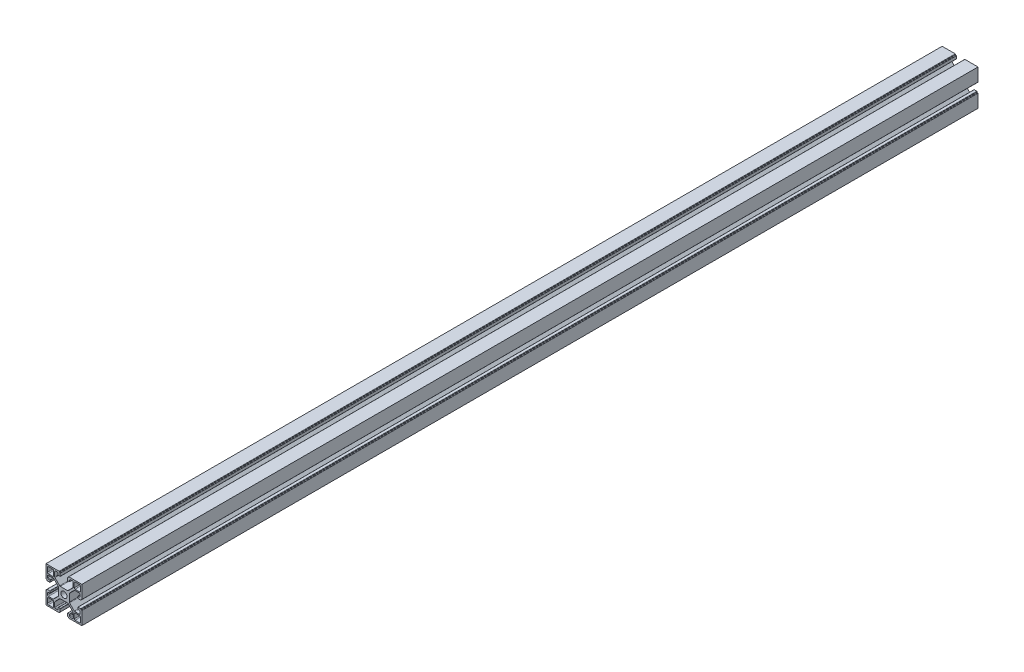
SolidWorks part; units mm, degrees
material "6063 T5"
ref_plane "Спереди" through (0, 0, 0) normal (0, 0, 1) x (1, 0, 0)
ref_plane "Сверху" through (0, 0, 0) normal (0, 1, 0) x (1, 0, 0)
ref_plane "Справа" through (0, 0, 0) normal (1, 0, 0) x (0, 0, -1)
sketch "Эскиз1" plane through (0, 0, 0) normal (0, 0, 1) x (1, 0, 0)
  line L0 (-19.98, 20.5457) -> (20.02, 20.5457) construction
  line L1 (-20, 10.25) -> (-20, 20)
  line L2 (-20, 20) -> (-10.25, 20)
  line L3 (10.25, 20) -> (20, 20)
  line L4 (-12.5, 11.5) -> (-17.5, 11.5)
  line L5 (-11.5, 12.5) -> (-11.5, 17.5)
  line L6 (-12.5, 18.5) -> (-17.5, 18.5)
  line L7 (-18.5, 12.5) -> (-18.5, 17.5)
  line L8 (20, 20) -> (20, 10.25)
  line L9 (11.5, 12.5) -> (11.5, 17.5)
  line L10 (12.5, 11.5) -> (17.5, 11.5)
  line L11 (18.5, 12.5) -> (18.5, 17.5)
  line L12 (12.5, 18.5) -> (17.5, 18.5)
  line L13 (20, -10.25) -> (20, -20)
  line L14 (20, -20) -> (10.25, -20)
  line L15 (12.5, -11.5) -> (17.5, -11.5)
  line L16 (11.5, -12.5) -> (11.5, -17.5)
  line L17 (12.5, -18.5) -> (17.5, -18.5)
  line L18 (18.5, -12.5) -> (18.5, -17.5)
  line L19 (-10.25, -20) -> (-20, -20)
  line L20 (-20, -20) -> (-20, -10.25)
  line L21 (-11.5, -12.5) -> (-11.5, -17.5)
  line L22 (-12.5, -11.5) -> (-17.5, -11.5)
  line L23 (-18.5, -12.5) -> (-18.5, -17.5)
  line L24 (-12.5, -18.5) -> (-17.5, -18.5)
  line L25 (0, 0) -> (-11.5, 12.5) construction
  line L26 (-20.032, 22.6558) -> (19.968, 22.6558) construction
  arc A1 (-17.5, 18.5) -> (-18.5, 17.5) centre (-17.5, 17.5) ccw
  arc A2 (-17.5, 11.5) -> (-18.5, 12.5) centre (-17.5, 12.5) cw
  arc A3 (-12.5, 11.5) -> (-11.5, 12.5) centre (-12.5, 12.5) ccw
  arc A4 (-11.5, 17.5) -> (-12.5, 18.5) centre (-12.5, 17.5) ccw
  circle A5 centre (0, 0) radius 3.4
  arc A7 (18.5, 17.5) -> (17.5, 18.5) centre (17.5, 17.5) ccw
  arc A8 (11.5, 17.5) -> (12.5, 18.5) centre (12.5, 17.5) cw
  arc A9 (11.5, 12.5) -> (12.5, 11.5) centre (12.5, 12.5) ccw
  arc A10 (17.5, 11.5) -> (18.5, 12.5) centre (17.5, 12.5) ccw
  arc A12 (17.5, -18.5) -> (18.5, -17.5) centre (17.5, -17.5) ccw
  arc A13 (17.5, -11.5) -> (18.5, -12.5) centre (17.5, -12.5) cw
  arc A14 (12.5, -11.5) -> (11.5, -12.5) centre (12.5, -12.5) ccw
  arc A15 (11.5, -17.5) -> (12.5, -18.5) centre (12.5, -17.5) ccw
  arc A17 (-18.5, -17.5) -> (-17.5, -18.5) centre (-17.5, -17.5) ccw
  arc A18 (-11.5, -17.5) -> (-12.5, -18.5) centre (-12.5, -17.5) cw
  arc A19 (-11.5, -12.5) -> (-12.5, -11.5) centre (-12.5, -12.5) ccw
  arc A20 (-17.5, -11.5) -> (-18.5, -12.5) centre (-17.5, -12.5) ccw
  point P5 (0, 0)
  line B0 (-20, 10.25) -> (-20, 5.4)
  line B1 (-19.7, 5.1) -> (-19.3, 5.1)
  line B2 (-19, 4.8) -> (-19, 4.4)
  line B3 (-18.7, 4.1) -> (-15.8, 4.1)
  line B4 (-15.5, 4.4) -> (-15.5, 6.1)
  line B5 (-15.8, 6.4) -> (-17.2, 6.4)
  line B6 (-18.2, 7.4) -> (-18.2, 9.25)
  line B7 (-17.2, 10.25) -> (-12.1642, 10.25)
  line B8 (-11.4571, 9.9571) -> (-6.2929, 4.7929)
  line B9 (-6, 4.0858) -> (-6, -4.0858)
  line B10 (-6, 0) -> (-20, 0) construction
  line B11 (-11.4571, -9.9571) -> (-6.2929, -4.7929)
  line B12 (-17.2, -10.25) -> (-12.1642, -10.25)
  line B13 (-18.2, -7.4) -> (-18.2, -9.25)
  line B14 (-15.8, -6.4) -> (-17.2, -6.4)
  line B15 (-15.5, -4.4) -> (-15.5, -6.1)
  line B16 (-18.7, -4.1) -> (-15.8, -4.1)
  line B17 (-19, -4.8) -> (-19, -4.4)
  line B18 (-19.7, -5.1) -> (-19.3, -5.1)
  line B19 (-20, -10.25) -> (-20, -5.4)
  arc B20 (-15.5, 6.1) -> (-15.8, 6.4) centre (-15.8, 6.1) ccw
  arc B21 (-15.8, 4.1) -> (-15.5, 4.4) centre (-15.8, 4.4) ccw
  arc B22 (-19, 4.4) -> (-18.7, 4.1) centre (-18.7, 4.4) ccw
  arc B23 (-19.3, 5.1) -> (-19, 4.8) centre (-19.3, 4.8) cw
  arc B24 (-20, 5.4) -> (-19.7, 5.1) centre (-19.7, 5.4) ccw
  arc B25 (-6.2929, 4.7929) -> (-6, 4.0858) centre (-7, 4.0858) cw
  arc B26 (-12.1642, 10.25) -> (-11.4571, 9.9571) centre (-12.1642, 9.25) cw
  arc B27 (-18.2, 9.25) -> (-17.2, 10.25) centre (-17.2, 9.25) cw
  arc B28 (-17.2, 6.4) -> (-18.2, 7.4) centre (-17.2, 7.4) cw
  arc B29 (-17.2, -6.4) -> (-18.2, -7.4) centre (-17.2, -7.4) ccw
  arc B30 (-18.2, -9.25) -> (-17.2, -10.25) centre (-17.2, -9.25) ccw
  arc B31 (-12.1642, -10.25) -> (-11.4571, -9.9571) centre (-12.1642, -9.25) ccw
  arc B32 (-6.2929, -4.7929) -> (-6, -4.0858) centre (-7, -4.0858) ccw
  arc B33 (-20, -5.4) -> (-19.7, -5.1) centre (-19.7, -5.4) cw
  arc B34 (-19.3, -5.1) -> (-19, -4.8) centre (-19.3, -4.8) ccw
  arc B35 (-19, -4.4) -> (-18.7, -4.1) centre (-18.7, -4.4) cw
  arc B36 (-15.8, -4.1) -> (-15.5, -4.4) centre (-15.8, -4.4) cw
  arc B37 (-15.5, -6.1) -> (-15.8, -6.4) centre (-15.8, -6.1) cw
  line B38 (10.25, 20) -> (5.4, 20)
  line B39 (5.1, 19.7) -> (5.1, 19.3)
  line B40 (4.8, 19) -> (4.4, 19)
  line B41 (4.1, 18.7) -> (4.1, 15.8)
  line B42 (4.4, 15.5) -> (6.1, 15.5)
  line B43 (6.4, 15.8) -> (6.4, 17.2)
  line B44 (7.4, 18.2) -> (9.25, 18.2)
  line B45 (10.25, 17.2) -> (10.25, 12.1642)
  line B46 (9.9571, 11.4571) -> (4.7929, 6.2929)
  line B47 (4.0858, 6) -> (-4.0858, 6)
  line B48 (0, 6) -> (0, 20) construction
  line B49 (-9.9571, 11.4571) -> (-4.7929, 6.2929)
  line B50 (-10.25, 17.2) -> (-10.25, 12.1642)
  line B51 (-7.4, 18.2) -> (-9.25, 18.2)
  line B52 (-6.4, 15.8) -> (-6.4, 17.2)
  line B53 (-4.4, 15.5) -> (-6.1, 15.5)
  line B54 (-4.1, 18.7) -> (-4.1, 15.8)
  line B55 (-4.8, 19) -> (-4.4, 19)
  line B56 (-5.1, 19.7) -> (-5.1, 19.3)
  line B57 (-10.25, 20) -> (-5.4, 20)
  arc B58 (6.1, 15.5) -> (6.4, 15.8) centre (6.1, 15.8) ccw
  arc B59 (4.1, 15.8) -> (4.4, 15.5) centre (4.4, 15.8) ccw
  arc B60 (4.4, 19) -> (4.1, 18.7) centre (4.4, 18.7) ccw
  arc B61 (5.1, 19.3) -> (4.8, 19) centre (4.8, 19.3) cw
  arc B62 (5.4, 20) -> (5.1, 19.7) centre (5.4, 19.7) ccw
  arc B63 (4.7929, 6.2929) -> (4.0858, 6) centre (4.0858, 7) cw
  arc B64 (10.25, 12.1642) -> (9.9571, 11.4571) centre (9.25, 12.1642) cw
  arc B65 (9.25, 18.2) -> (10.25, 17.2) centre (9.25, 17.2) cw
  arc B66 (6.4, 17.2) -> (7.4, 18.2) centre (7.4, 17.2) cw
  arc B67 (-6.4, 17.2) -> (-7.4, 18.2) centre (-7.4, 17.2) ccw
  arc B68 (-9.25, 18.2) -> (-10.25, 17.2) centre (-9.25, 17.2) ccw
  arc B69 (-10.25, 12.1642) -> (-9.9571, 11.4571) centre (-9.25, 12.1642) ccw
  arc B70 (-4.7929, 6.2929) -> (-4.0858, 6) centre (-4.0858, 7) ccw
  arc B71 (-5.4, 20) -> (-5.1, 19.7) centre (-5.4, 19.7) cw
  arc B72 (-5.1, 19.3) -> (-4.8, 19) centre (-4.8, 19.3) ccw
  arc B73 (-4.4, 19) -> (-4.1, 18.7) centre (-4.4, 18.7) cw
  arc B74 (-4.1, 15.8) -> (-4.4, 15.5) centre (-4.4, 15.8) cw
  arc B75 (-6.1, 15.5) -> (-6.4, 15.8) centre (-6.1, 15.8) cw
  line B76 (20, -10.25) -> (20, -5.4)
  line B77 (19.7, -5.1) -> (19.3, -5.1)
  line B78 (19, -4.8) -> (19, -4.4)
  line B79 (18.7, -4.1) -> (15.8, -4.1)
  line B80 (15.5, -4.4) -> (15.5, -6.1)
  line B81 (15.8, -6.4) -> (17.2, -6.4)
  line B82 (18.2, -7.4) -> (18.2, -9.25)
  line B83 (17.2, -10.25) -> (12.1642, -10.25)
  line B84 (11.4571, -9.9571) -> (6.2929, -4.7929)
  line B85 (6, -4.0858) -> (6, 4.0858)
  line B86 (6, 0) -> (20, 0) construction
  line B87 (11.4571, 9.9571) -> (6.2929, 4.7929)
  line B88 (17.2, 10.25) -> (12.1642, 10.25)
  line B89 (18.2, 7.4) -> (18.2, 9.25)
  line B90 (15.8, 6.4) -> (17.2, 6.4)
  line B91 (15.5, 4.4) -> (15.5, 6.1)
  line B92 (18.7, 4.1) -> (15.8, 4.1)
  line B93 (19, 4.8) -> (19, 4.4)
  line B94 (19.7, 5.1) -> (19.3, 5.1)
  line B95 (20, 10.25) -> (20, 5.4)
  arc B96 (15.5, -6.1) -> (15.8, -6.4) centre (15.8, -6.1) ccw
  arc B97 (15.8, -4.1) -> (15.5, -4.4) centre (15.8, -4.4) ccw
  arc B98 (19, -4.4) -> (18.7, -4.1) centre (18.7, -4.4) ccw
  arc B99 (19.3, -5.1) -> (19, -4.8) centre (19.3, -4.8) cw
  arc B100 (20, -5.4) -> (19.7, -5.1) centre (19.7, -5.4) ccw
  arc B101 (6.2929, -4.7929) -> (6, -4.0858) centre (7, -4.0858) cw
  arc B102 (12.1642, -10.25) -> (11.4571, -9.9571) centre (12.1642, -9.25) cw
  arc B103 (18.2, -9.25) -> (17.2, -10.25) centre (17.2, -9.25) cw
  arc B104 (17.2, -6.4) -> (18.2, -7.4) centre (17.2, -7.4) cw
  arc B105 (17.2, 6.4) -> (18.2, 7.4) centre (17.2, 7.4) ccw
  arc B106 (18.2, 9.25) -> (17.2, 10.25) centre (17.2, 9.25) ccw
  arc B107 (12.1642, 10.25) -> (11.4571, 9.9571) centre (12.1642, 9.25) ccw
  arc B108 (6.2929, 4.7929) -> (6, 4.0858) centre (7, 4.0858) ccw
  arc B109 (20, 5.4) -> (19.7, 5.1) centre (19.7, 5.4) cw
  arc B110 (19.3, 5.1) -> (19, 4.8) centre (19.3, 4.8) ccw
  arc B111 (19, 4.4) -> (18.7, 4.1) centre (18.7, 4.4) cw
  arc B112 (15.8, 4.1) -> (15.5, 4.4) centre (15.8, 4.4) cw
  arc B113 (15.5, 6.1) -> (15.8, 6.4) centre (15.8, 6.1) cw
  line B114 (-10.25, -20) -> (-5.4, -20)
  line B115 (-5.1, -19.7) -> (-5.1, -19.3)
  line B116 (-4.8, -19) -> (-4.4, -19)
  line B117 (-4.1, -18.7) -> (-4.1, -15.8)
  line B118 (-4.4, -15.5) -> (-6.1, -15.5)
  line B119 (-6.4, -15.8) -> (-6.4, -17.2)
  line B120 (-7.4, -18.2) -> (-9.25, -18.2)
  line B121 (-10.25, -17.2) -> (-10.25, -12.1642)
  line B122 (-9.9571, -11.4571) -> (-4.7929, -6.2929)
  line B123 (-4.0858, -6) -> (4.0858, -6)
  line B124 (0, -6) -> (0, -20) construction
  line B125 (9.9571, -11.4571) -> (4.7929, -6.2929)
  line B126 (10.25, -17.2) -> (10.25, -12.1642)
  line B127 (7.4, -18.2) -> (9.25, -18.2)
  line B128 (6.4, -15.8) -> (6.4, -17.2)
  line B129 (4.4, -15.5) -> (6.1, -15.5)
  line B130 (4.1, -18.7) -> (4.1, -15.8)
  line B131 (4.8, -19) -> (4.4, -19)
  line B132 (5.1, -19.7) -> (5.1, -19.3)
  line B133 (10.25, -20) -> (5.4, -20)
  arc B134 (-6.1, -15.5) -> (-6.4, -15.8) centre (-6.1, -15.8) ccw
  arc B135 (-4.1, -15.8) -> (-4.4, -15.5) centre (-4.4, -15.8) ccw
  arc B136 (-4.4, -19) -> (-4.1, -18.7) centre (-4.4, -18.7) ccw
  arc B137 (-5.1, -19.3) -> (-4.8, -19) centre (-4.8, -19.3) cw
  arc B138 (-5.4, -20) -> (-5.1, -19.7) centre (-5.4, -19.7) ccw
  arc B139 (-4.7929, -6.2929) -> (-4.0858, -6) centre (-4.0858, -7) cw
  arc B140 (-10.25, -12.1642) -> (-9.9571, -11.4571) centre (-9.25, -12.1642) cw
  arc B141 (-9.25, -18.2) -> (-10.25, -17.2) centre (-9.25, -17.2) cw
  arc B142 (-6.4, -17.2) -> (-7.4, -18.2) centre (-7.4, -17.2) cw
  arc B143 (6.4, -17.2) -> (7.4, -18.2) centre (7.4, -17.2) ccw
  arc B144 (9.25, -18.2) -> (10.25, -17.2) centre (9.25, -17.2) ccw
  arc B145 (10.25, -12.1642) -> (9.9571, -11.4571) centre (9.25, -12.1642) ccw
  arc B146 (4.7929, -6.2929) -> (4.0858, -6) centre (4.0858, -7) ccw
  arc B147 (5.4, -20) -> (5.1, -19.7) centre (5.4, -19.7) cw
  arc B148 (5.1, -19.3) -> (4.8, -19) centre (4.8, -19.3) ccw
  arc B149 (4.4, -19) -> (4.1, -18.7) centre (4.4, -18.7) cw
  arc B150 (4.1, -15.8) -> (4.4, -15.5) centre (4.4, -15.8) cw
  arc B151 (6.1, -15.5) -> (6.4, -15.8) centre (6.1, -15.8) cw
  dimension "D2" = 1.5
  dimension "D3" = 1
  dimension "D5" = 1
  dimension "D6" = 6.8
  dimension "D1" = 20
  dimension "D4" = 7
  dimension "D7" = 40
  dimension "D8" = 4
  dimension "D9" = 1.5
sketch_block_instance "8B(20,5PL)-1"
sketch_block "8B(20,5PL)" parameters "D7"=0.3, "D8"=1, "D1"=14, "D2"=4.5, "D3"=8.2, "D4"=20.5, "D5"=10.2, "D6"=135, "D9"=11.8, "D10"=4.85, "D11"=1.2, "D12"=1.85
sketch_block_instance "8B(20,5PL)-3"
sketch_block_instance "8B(20,5PL)-4"
sketch_block_instance "8B(20,5PL)-5"
extrude "Бобышка-Вытянуть1" add sketch "Эскиз1" along normal blind 1000
